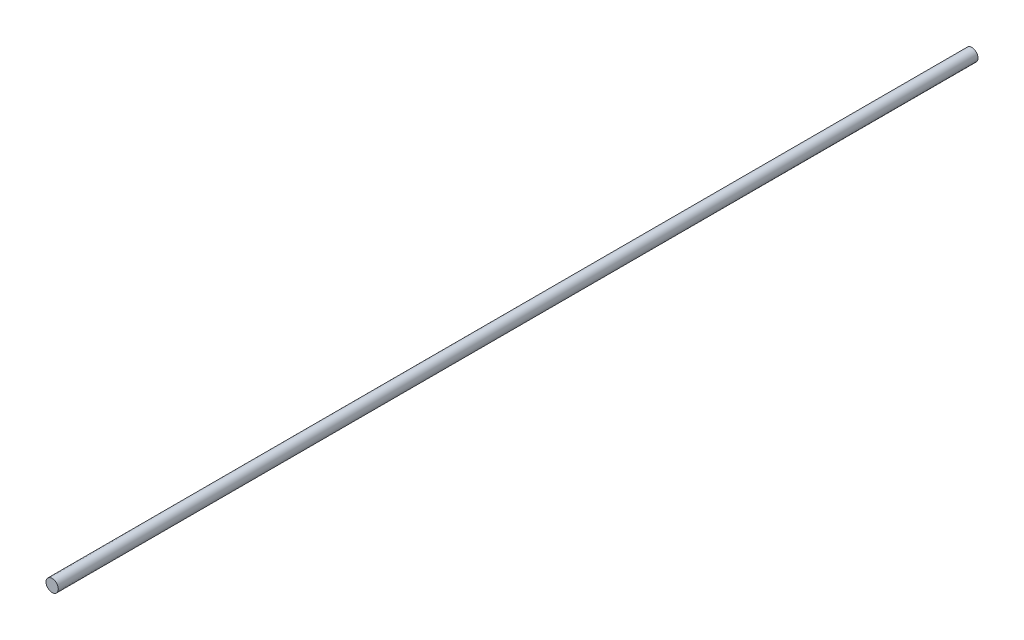
SolidWorks part; units mm, degrees
ref_plane "Front Plane" through (0, 0, 0) normal (0, 0, 1) x (1, 0, 0)
ref_plane "Top Plane" through (0, 0, 0) normal (0, 1, 0) x (1, 0, 0)
ref_plane "Right Plane" through (0, 0, 0) normal (1, 0, 0) x (0, 0, -1)
sketch "Sketch1" plane through (0, 0, 0) normal (0, 0, 1) x (1, 0, 0)
  circle A0 centre (0, 0) radius 3.175
  dimension "D1" = 6.35
extrude "Boss-Extrude1" add sketch "Sketch1" along normal blind 475
